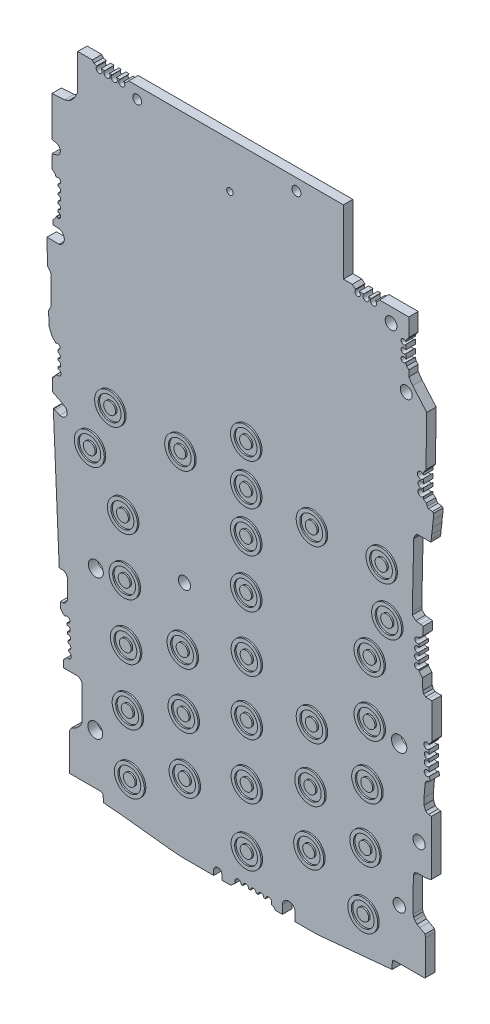
SolidWorks part; units mm, degrees
material "Plastique personnalisé"
ref_plane "Plan de face" through (0, 0, 0) normal (0, 0, 1) x (1, 0, 0)
ref_plane "Plan de dessus" through (0, 0, 0) normal (0, 1, 0) x (1, 0, 0)
ref_plane "Plan de droite" through (0, 0, 0) normal (1, 0, 0) x (0, 0, -1)
sketch "pcbmain" plane through (0, 0, 0) normal (0, 0, 1) x (1, 0, 0)
  line L0 (-26.3476, 56.3002) -> (18.5524, 56.3002) construction
  line L1 (-26.3472, 56.3293) -> (-23.9276, 56.3293)
  line L2 (18.595, 45.4298) -> (20.1113, 45.4298)
  line L3 (18.595, 56.3293) -> (18.595, 45.4298)
  line L4 (29.6758, 45.4298) -> (29.6758, 42.4054)
  line L5 (29.6758, 36.6277) -> (30.333, 35.6864)
  line L6 (30.333, 35.6864) -> (32.1199, 33.6174)
  line L7 (32.1199, 33.6174) -> (32.7131, 32.9305)
  line L8 (32.7131, 32.9305) -> (32.5843, 24.4781)
  line L9 (32.5843, 24.4781) -> (32.1653, 23.839)
  line L10 (32.1653, 23.839) -> (32.1653, 23.4305)
  line L11 (32.1653, 20.2857) -> (32.1653, 19.9086)
  line L12 (32.1653, 19.9086) -> (32.6305, 19.6035)
  line L13 (32.6305, 19.6035) -> (32.804, 19.1871)
  line L14 (33.0248, 18.9629) -> (33.6866, 18.8922)
  line L15 (33.6866, 18.8922) -> (33.876, 18.717)
  line L16 (33.876, 18.717) -> (33.876, 17.8058)
  line L17 (33.876, 17.8058) -> (33.7813, 17.8058)
  line L18 (33.7813, 17.8058) -> (33.7082, 16.5757)
  line L19 (33.7082, 16.5757) -> (33.5539, 15.419)
  line L20 (33.5539, 15.419) -> (33.4978, 14.7416)
  line L21 (33.4978, 14.7416) -> (33.4001, 14.2515)
  line L22 (33.4001, 14.2515) -> (31.0026, 14.2515)
  line L23 (31.0026, 14.2515) -> (30.6972, 13.7858)
  line L24 (30.6972, 13.7858) -> (30.5206, 13.3921)
  line L25 (30.5206, 13.3921) -> (30.506, 13.216)
  line L26 (30.506, 13.216) -> (30.2731, 2.4736)
  line L27 (30.2731, 2.4736) -> (30.2731, 1.9888)
  line L28 (30.2731, 1.9888) -> (30.5221, 1.7586)
  line L29 (30.5221, 1.7586) -> (30.8499, 1.4554)
  line L30 (30.8499, 1.4554) -> (31.0993, 1.4057)
  line L31 (31.0993, 1.4057) -> (31.6928, 1.3565)
  line L32 (31.6928, 1.3565) -> (32.1199, 1.2715)
  line L33 (32.1199, 1.2715) -> (32.1199, -0.1245)
  line L34 (32.1199, -0.1245) -> (31.8538, -0.3542)
  line L35 (31.8538, -0.3542) -> (31.7258, -0.5495)
  line L36 (31.7258, -0.5495) -> (31.3961, -0.6869)
  line L37 (31.3961, -0.6869) -> (31.3961, -0.9137)
  line L38 (31.3961, -5.654) -> (31.9868, -6.338)
  line L39 (31.9868, -6.338) -> (32.0491, -8.1942)
  line L40 (32.0491, -8.1942) -> (32.2013, -8.6516)
  line L41 (32.2013, -8.6516) -> (32.5523, -8.8818)
  line L42 (32.5523, -8.8818) -> (32.9753, -8.9168)
  line L43 (32.9753, -8.9168) -> (33.6311, -8.9168)
  line L44 (33.6311, -8.9168) -> (33.6311, -14.8864)
  line L45 (33.6311, -14.8864) -> (33.1333, -15.5093)
  line L46 (33.1333, -15.5093) -> (33.1333, -15.6135)
  line L47 (33.1333, -20.2606) -> (33.3188, -20.8179)
  line L48 (33.3188, -20.8179) -> (33.1333, -20.9781)
  line L49 (33.1333, -20.9781) -> (32.7638, -21.1012)
  line L50 (32.7638, -21.1012) -> (32.4789, -21.4576)
  line L51 (32.4789, -21.4576) -> (32.43, -21.7035)
  line L52 (32.43, -21.7035) -> (32.2548, -23.8175)
  line L53 (32.2548, -23.8175) -> (32.2548, -24.9106)
  line L54 (32.2548, -24.9106) -> (32.5523, -25.6246)
  line L55 (32.5523, -25.6246) -> (33.0248, -25.8955)
  line L56 (33.0248, -25.8955) -> (33.4978, -25.9347)
  line L57 (33.4978, -25.9347) -> (33.4978, -35.191)
  line L58 (33.4978, -35.191) -> (33.1823, -35.3224)
  line L59 (33.1823, -35.3224) -> (32.5523, -35.4198)
  line L60 (32.5523, -35.4198) -> (31.0993, -35.4198)
  line L61 (31.0993, -35.4198) -> (30.686, -35.5921)
  line L62 (30.686, -35.5921) -> (30.4941, -35.9268)
  line L63 (30.4941, -35.9268) -> (30.4394, -36.2015)
  line L64 (30.4394, -36.2015) -> (30.3976, -41.7883)
  line L65 (30.3976, -41.7883) -> (30.4941, -42.2439)
  line L66 (30.4941, -42.2439) -> (30.7305, -42.5825)
  line L67 (30.7305, -42.5825) -> (31.0716, -42.9775)
  line L68 (31.0716, -42.9775) -> (31.534, -43.2426)
  line L69 (31.534, -43.2426) -> (32.43, -43.7347)
  line L70 (32.43, -43.7347) -> (32.5255, -44.1857)
  line L71 (32.5255, -44.1857) -> (32.4811, -50.1182)
  line L72 (32.4811, -50.1182) -> (32.3424, -50.215)
  line L73 (32.3424, -50.215) -> (27.1201, -50.215)
  line L74 (27.1201, -50.215) -> (26.9245, -50.384)
  line L75 (26.9245, -50.384) -> (26.8778, -50.6183)
  line L76 (26.8778, -50.6183) -> (26.854, -51.7168)
  line L77 (26.854, -51.7168) -> (14.0715, -52.9243)
  line L78 (14.0715, -52.9243) -> (12.4897, -52.9243)
  line L79 (12.4897, -52.9243) -> (10.4248, -52.9243)
  line L80 (10.4248, -52.9243) -> (10.4248, -51.5129)
  line L82 (8.2651, -51.5129) -> (8.2651, -52.9243)
  line L83 (8.2651, -52.9243) -> (7.0763, -52.9243)
  line L84 (7.0763, -52.9243) -> (6.7493, -52.5455)
  line L85 (6.7493, -52.5455) -> (6.4591, -52.4154)
  line L86 (6.4591, -52.4154) -> (6.4591, -52.0567)
  line L87 (5.429, -52.0567) -> (5.0907, -52.0567)
  line L88 (0.2185, -52.0567) -> (0.2185, -52.4154)
  line L89 (0.2185, -52.4154) -> (-0.4956, -53.0321)
  line L90 (-0.4956, -53.0321) -> (-1.9859, -53.0321)
  line L91 (-1.9859, -53.0321) -> (-1.9859, -52.236)
  line L93 (-3.3634, -52.236) -> (-3.3634, -53.0321)
  line L94 (-3.3634, -53.0321) -> (-8.7561, -53.0321)
  line L95 (-8.7561, -53.0321) -> (-11.0114, -52.8452)
  line L96 (-11.0114, -52.8452) -> (-17.1621, -52.1575)
  line L97 (-17.1621, -52.1575) -> (-19.1333, -51.937)
  line L98 (-19.1333, -51.937) -> (-21.3313, -51.7549)
  line L99 (-21.3313, -51.7549) -> (-22.056, -51.6739)
  line L100 (-22.056, -51.6739) -> (-22.0902, -50.6556)
  line L101 (-22.0902, -50.6556) -> (-22.1767, -50.448)
  line L102 (-22.1767, -50.448) -> (-22.3284, -50.3267)
  line L103 (-22.3284, -50.3267) -> (-22.6489, -50.2629)
  line L104 (-22.6489, -50.2629) -> (-27.796, -50.2629)
  line L105 (-27.796, -50.2629) -> (-27.796, -43.9395)
  line L106 (-27.796, -43.9395) -> (-27.4814, -43.4597)
  line L107 (-27.4814, -43.4597) -> (-27.0528, -43.2426)
  line L108 (-27.0528, -43.2426) -> (-26.7348, -43.11)
  line L109 (-26.7348, -43.11) -> (-26.2801, -42.6873)
  line L110 (-26.2801, -42.6873) -> (-25.9044, -42.2809)
  line L111 (-25.9044, -42.2809) -> (-25.7484, -41.9332)
  line L112 (-25.7484, -41.9332) -> (-25.6965, -41.8175)
  line L113 (-25.6965, -41.8175) -> (-25.653, -35.9963)
  line L114 (-25.653, -35.9963) -> (-25.7326, -35.8052)
  line L115 (-25.7326, -35.8052) -> (-25.9044, -35.6064)
  line L116 (-25.9044, -35.6064) -> (-26.0562, -35.4659)
  line L117 (-26.0562, -35.4659) -> (-26.1749, -35.3711)
  line L118 (-26.1749, -35.3711) -> (-26.3472, -35.2938)
  line L119 (-26.3472, -35.2938) -> (-28.8359, -35.2938)
  line L120 (-28.8359, -35.2938) -> (-28.8359, -34.1043)
  line L121 (-28.8359, -34.1043) -> (-28.4975, -33.812)
  line L122 (-28.4975, -33.812) -> (-28.2801, -33.54)
  line L123 (-28.2801, -33.54) -> (-28.1038, -33.5233)
  line L124 (-28.1038, -33.5233) -> (-27.8558, -33.5233)
  line L125 (-27.9317, -32.4351) -> (-27.9505, -32.1647)
  line L126 (-28.2801, -27.4401) -> (-28.6667, -27.6012)
  line L127 (-28.6667, -27.6012) -> (-28.8059, -27.4401)
  line L128 (-28.8059, -27.4401) -> (-29.3011, -26.8667)
  line L129 (-29.3011, -26.8667) -> (-29.3011, -25.7861)
  line L130 (-29.3011, -25.7861) -> (-28.8822, -25.7861)
  line L131 (-28.8822, -25.7861) -> (-28.5457, -25.6459)
  line L132 (-28.5457, -25.6459) -> (-28.3448, -25.4286)
  line L133 (-28.3448, -25.4286) -> (-28.1621, -25.0959)
  line L134 (-28.1621, -25.0959) -> (-28.1402, -24.9862)
  line L135 (-28.1402, -24.9862) -> (-28.1402, -21.7303)
  line L136 (-28.1402, -21.7303) -> (-28.2018, -21.5453)
  line L137 (-28.2018, -21.5453) -> (-28.3568, -21.3025)
  line L138 (-28.3568, -21.3025) -> (-28.5305, -21.1418)
  line L139 (-28.5305, -21.1418) -> (-28.6817, -21.0588)
  line L140 (-28.6817, -21.0588) -> (-28.8654, -21.0019)
  line L141 (-28.8654, -21.0019) -> (-29.4497, -21.0019)
  line L142 (-29.4497, -21.0019) -> (-29.5384, -20.8993)
  line L143 (-29.5384, -20.8993) -> (-30.539, 1.9081)
  line L144 (-30.539, 1.9081) -> (-30.4443, 1.9081)
  line L145 (-30.4443, 1.9081) -> (-30.2416, 1.7968)
  line L147 (-29.2742, 3.5581) -> (-30.6939, 4.2682)
  line L148 (-30.6939, 4.2682) -> (-30.716, 5.2591)
  line L149 (-30.716, 5.2591) -> (-30.716, 6.3629)
  line L150 (-30.716, 6.3629) -> (-30.548, 6.4188)
  line L151 (-30.548, 6.4188) -> (-30.1481, 6.8512)
  line L152 (-30.1481, 6.8512) -> (-30.0803, 7.0704)
  line L153 (-30.0803, 7.0704) -> (-30.0057, 7.118)
  line L154 (-30.0057, 7.118) -> (-29.7579, 7.118)
  line L155 (-29.7579, 8.0616) -> (-29.7579, 8.3754)
  line L156 (-29.7579, 11.8098) -> (-30.1273, 11.6869)
  line L157 (-30.1273, 11.6869) -> (-30.632, 12.2713)
  line L158 (-30.632, 12.2713) -> (-30.8474, 12.5207)
  line L159 (-30.8474, 12.5207) -> (-30.9767, 12.909)
  line L160 (-30.9767, 12.909) -> (-31.2457, 13.5545)
  line L161 (-31.2457, 13.5545) -> (-31.3467, 15.8567)
  line L162 (-31.3467, 15.8567) -> (-31.0827, 16.3846)
  line L163 (-31.0827, 16.3846) -> (-30.9593, 16.5636)
  line L164 (-30.9593, 16.5636) -> (-30.9593, 21.4877)
  line L165 (-30.9593, 21.4877) -> (-31.0481, 21.7006)
  line L166 (-31.0481, 21.7006) -> (-31.2804, 22.0359)
  line L167 (-31.2804, 22.0359) -> (-31.5199, 22.2878)
  line L168 (-31.5199, 22.2878) -> (-31.6133, 26.4777)
  line L169 (-31.6133, 26.4777) -> (-29.5384, 26.4777)
  line L171 (-29.5384, 28.7595) -> (-30.6062, 28.788)
  line L172 (-30.6062, 28.788) -> (-30.6062, 29.5385)
  line L173 (-30.6062, 29.5385) -> (-30.1378, 30.045)
  line L174 (-30.1378, 30.045) -> (-30.0597, 30.2974)
  line L175 (-30.0597, 30.2974) -> (-29.9426, 30.2974)
  line L176 (-29.9426, 30.2974) -> (-29.7525, 30.2023)
  line L177 (-29.7525, 30.2023) -> (-29.7082, 30.2023)
  line L178 (-29.7082, 31.0839) -> (-29.7082, 31.5125)
  line L179 (-29.7082, 36.2036) -> (-30.0597, 36.0571)
  line L180 (-30.0597, 36.0571) -> (-30.2416, 36.4937)
  line L181 (-30.2416, 36.4937) -> (-30.4917, 36.7249)
  line L182 (-30.4917, 36.7249) -> (-30.7397, 36.849)
  line L183 (-30.7397, 36.849) -> (-30.716, 39.2001)
  line L184 (-30.716, 39.2001) -> (-30.4443, 39.219)
  line L185 (-30.4443, 39.219) -> (-30.1506, 39.3168)
  line L187 (-30.1506, 41.1223) -> (-30.4708, 41.1861)
  line L188 (-30.4708, 41.1861) -> (-30.7633, 41.2444)
  line L189 (-30.7633, 41.2444) -> (-30.7817, 41.2614)
  line L190 (-30.7817, 41.2614) -> (-30.7817, 47.9834)
  line L191 (-30.7817, 47.9834) -> (-28.6061, 48.1351)
  line L192 (-28.6061, 48.1351) -> (-27.9329, 48.3593)
  line L193 (-27.9329, 48.3593) -> (-27.3741, 48.7463)
  line L194 (-27.3741, 48.7463) -> (-26.9107, 49.3263)
  line L195 (-26.9107, 49.3263) -> (-26.6074, 49.9325)
  line L196 (-26.6074, 49.9325) -> (-26.4023, 50.3426)
  line L197 (-26.4023, 50.3426) -> (-26.4023, 56.3293)
  line L198 (-26.4023, 56.3293) -> (-26.3472, 56.3293)
  line L199 (-29.7082, 32.3376) -> (-29.7082, 32.7575)
  line L200 (-29.7082, 33.5925) -> (-29.7082, 33.935)
  line L201 (-29.7082, 34.8538) -> (-29.7082, 35.2532)
  line L202 (-29.7579, 10.5366) -> (-29.7579, 10.9255)
  line L203 (-29.7579, 9.3433) -> (-29.7579, 9.6306)
  line L204 (-29.2742, 3.5581) -> (-28.714, 3.2243)
  line L205 (-30.2416, 1.7968) -> (-29.4497, 1.4304)
  line L206 (-28.1894, -28.7393) -> (-28.2141, -28.3852)
  line L207 (-28.1, -30.0214) -> (-28.1266, -29.6408)
  line L208 (-28.0144, -31.2488) -> (-28.0402, -30.8797)
  line L209 (1.5746, -52.0567) -> (1.2979, -52.0567)
  line L210 (2.8868, -52.0567) -> (2.5382, -52.0567)
  line L211 (4.1681, -52.0567) -> (3.7735, -52.0567)
  line L212 (33.1333, -16.2809) -> (33.1333, -17.0014)
  line L213 (33.1333, -17.638) -> (33.1333, -18.1861)
  line L214 (33.1333, -18.8447) -> (33.1333, -19.6226)
  line L215 (31.3961, -5.4452) -> (31.3961, -5.654)
  line L216 (31.3961, -4.0963) -> (31.3961, -4.7104)
  line L217 (31.3961, -2.9315) -> (31.3961, -3.4257)
  line L218 (31.3961, -1.6844) -> (31.3961, -2.2197)
  line L219 (32.1653, 22.9543) -> (32.1653, 22.1563)
  line L220 (32.1653, 21.6104) -> (32.1481, 20.9645)
  line L221 (29.6758, 42.4054) -> (29.1821, 41.7726)
  line L222 (29.1821, 41.7726) -> (29.1821, 41.5324)
  line L223 (29.1821, 38.4338) -> (29.2984, 37.9974)
  line L224 (29.2984, 37.9974) -> (29.6758, 37.6555)
  line L225 (29.6758, 37.6555) -> (29.6758, 36.6277)
  line L226 (29.1821, 38.4923) -> (29.1821, 38.4338)
  line L227 (29.1821, 39.7817) -> (29.1821, 38.9651)
  line L228 (29.1821, 41.157) -> (29.1821, 40.3433)
  line L229 (20.1113, 45.4298) -> (20.6301, 44.9722)
  line L230 (20.6301, 44.9722) -> (20.7217, 44.9722)
  line L231 (24.0446, 44.9722) -> (24.4312, 45.0502)
  line L232 (24.4312, 45.0502) -> (24.7058, 45.4298)
  line L233 (24.7058, 45.4298) -> (29.6758, 45.4298)
  line L234 (22.8375, 44.9722) -> (23.3258, 44.9722)
  line L235 (21.2642, 44.9722) -> (22.0339, 44.9722)
  line L236 (-23.9276, 56.3293) -> (-23.6646, 55.9528)
  line L237 (-23.6646, 55.9528) -> (-23.2013, 55.8026)
  line L238 (-23.2013, 55.8026) -> (-23.1282, 55.8026)
  line L239 (-18.6306, 55.8026) -> (-18.28, 55.8026)
  line L240 (-18.28, 55.8026) -> (-17.7728, 56.3293)
  line L241 (-17.7728, 56.3293) -> (18.595, 56.3293)
  line L242 (-19.857, 55.8026) -> (-19.2665, 55.8026)
  line L243 (-21.0361, 55.8026) -> (-20.5919, 55.8026)
  line L244 (-22.4342, 55.8026) -> (-21.8283, 55.8026)
  line L245 (32.1481, 20.2857) -> (32.1653, 20.2857)
  arc A0 (32.804, 19.1871) -> (33.0248, 18.9629) centre (33.1926, 19.349) ccw
  circle A1 centre (-16.3223, 54.33) radius 0.7602
  circle A2 centre (10.6479, 54.3822) radius 0.7591
  circle A3 centre (26.6739, 43.0034) radius 0.9966
  circle A4 centre (29.24, 34.1762) radius 1.0128
  circle A5 centre (-0.618, 48.6766) radius 0.5512
  circle A6 centre (-8.3261, -12.5822) radius 1.0254
  circle A7 centre (31.417, -30.7219) radius 1.0323
  circle A8 centre (28.062, -41.6944) radius 1.0418
  circle A9 centre (-23.4265, -41.7117) radius 1.257
  circle A10 centre (-23.3399, -17.9875) radius 1.2695
  circle A11 centre (28.0374, -17.9774) radius 1.2998
  arc A12 (-30.1506, 41.1223) -> (-30.1506, 39.3168) centre (-30.2618, 40.2196) cw
  arc A13 (-29.7082, 36.2036) -> (-29.7082, 35.2532) centre (-29.7648, 35.7284) cw
  arc A14 (-29.7082, 34.8538) -> (-29.7082, 33.935) centre (-29.7479, 34.3944) cw
  arc A15 (-29.7082, 33.5925) -> (-29.7082, 32.7575) centre (-29.7082, 33.175) cw
  arc A16 (-29.7082, 32.3376) -> (-29.7082, 31.5125) centre (-29.7082, 31.925) cw
  arc A17 (-29.7082, 31.0839) -> (-29.7082, 30.2023) centre (-29.7359, 30.6431) cw
  arc A18 (-29.5384, 28.7595) -> (-29.5384, 26.4777) centre (-29.861, 27.6186) cw
  arc A19 (-29.7579, 11.8098) -> (-29.7579, 10.9255) centre (-29.8293, 11.3677) cw
  arc A20 (-29.7579, 10.5366) -> (-29.7579, 9.6306) centre (-29.8009, 10.0836) cw
  arc A21 (-29.7579, 9.3433) -> (-29.7579, 8.3754) centre (-29.7681, 8.8594) cw
  arc A22 (-29.7579, 8.0616) -> (-29.7579, 7.118) centre (-29.7109, 7.5898) cw
  arc A23 (-28.714, 3.2243) -> (-29.4497, 1.4304) centre (-29.1748, 2.3655) cw
  arc A24 (-28.2801, -27.4401) -> (-28.2141, -28.3852) centre (-28.1992, -27.9093) cw
  arc A25 (-28.1894, -28.7393) -> (-28.1266, -29.6408) centre (-28.1244, -29.1877) cw
  arc A26 (-28.1, -30.0214) -> (-28.0402, -30.8797) centre (-28.0411, -30.4485) cw
  arc A27 (-28.0144, -31.2488) -> (-27.9505, -32.1647) centre (-28.0281, -31.7099) cw
  arc A28 (-27.9317, -32.4351) -> (-27.8558, -33.5233) centre (-28.079, -32.9921) cw
  arc A29 (-3.3634, -52.236) -> (-1.9859, -52.236) centre (-2.6747, -52.1987) cw
  arc A30 (0.2185, -52.0567) -> (1.2979, -52.0567) centre (0.7582, -52.0361) cw
  arc A31 (1.5746, -52.0567) -> (2.5382, -52.0567) centre (2.0564, -51.9987) cw
  arc A32 (2.8868, -52.0567) -> (3.7735, -52.0567) centre (3.3301, -51.9945) cw
  arc A33 (4.1681, -52.0567) -> (5.0907, -52.0567) centre (4.6294, -52.0122) cw
  arc A34 (5.429, -52.0567) -> (6.4591, -52.0567) centre (5.944, -52.0459) cw
  arc A35 (8.2651, -51.5129) -> (10.4248, -51.5129) centre (9.345, -51.5311) cw
  arc A36 (33.1333, -15.6135) -> (33.1333, -16.2809) centre (32.7495, -15.9472) ccw
  arc A37 (33.1333, -17.0014) -> (33.1333, -17.638) centre (32.781, -17.3197) ccw
  arc A38 (33.1333, -18.1861) -> (33.1333, -18.8447) centre (32.7816, -18.5154) ccw
  arc A39 (33.1333, -19.6226) -> (33.1333, -20.2606) centre (32.7675, -19.9416) ccw
  arc A40 (31.3961, -0.9137) -> (31.3961, -1.6844) centre (31.1428, -1.299) ccw
  arc A41 (31.3961, -2.9315) -> (31.3961, -2.2197) centre (31.1086, -2.5756) cw
  arc A42 (31.3961, -5.4452) -> (31.3961, -4.7104) centre (31.1107, -5.0778) cw
  arc A43 (31.3961, -4.0963) -> (31.3961, -3.4257) centre (31.0925, -3.761) cw
  arc A44 (32.1653, 23.4305) -> (32.1653, 22.9543) centre (31.678, 23.1924) ccw
  arc A45 (32.1653, 22.1563) -> (32.1653, 21.6104) centre (31.7325, 21.8834) ccw
  arc A46 (32.1481, 20.9645) -> (32.1481, 20.2857) centre (31.7418, 20.6251) ccw
  arc A47 (29.1821, 41.5324) -> (29.1821, 41.157) centre (28.7945, 41.3447) ccw
  arc A48 (29.1821, 40.3433) -> (29.1821, 39.7817) centre (28.8184, 40.0625) ccw
  arc A49 (29.1821, 38.9651) -> (29.1821, 38.4923) centre (28.8108, 38.7287) ccw
  arc A50 (20.7217, 44.9722) -> (21.2642, 44.9722) centre (20.9929, 44.5846) ccw
  arc A51 (22.0339, 44.9722) -> (22.8375, 44.9722) centre (22.4357, 44.6188) ccw
  arc A52 (23.3258, 44.9722) -> (24.0446, 44.9722) centre (23.6852, 44.5848) ccw
  arc A53 (-23.1282, 55.8026) -> (-22.4342, 55.8026) centre (-22.7812, 55.4353) ccw
  arc A54 (-21.8283, 55.8026) -> (-21.0361, 55.8026) centre (-21.4322, 55.444) ccw
  arc A55 (-20.5919, 55.8026) -> (-19.857, 55.8026) centre (-20.2245, 55.4206) ccw
  arc A56 (-19.2665, 55.8026) -> (-18.6306, 55.8026) centre (-18.9486, 55.3964) ccw
  dimension "D1" = 44.9
sketch "buttons" plane through (0, 0, 0) normal (0, 0, 1) x (1, 0, 0)
  circle A0 centre (2.268, 13.4844) radius 1.0026
  circle A1 centre (2.268, 13.4844) radius 1.939
  circle A2 centre (2.268, 13.4844) radius 2.542
  circle A3 centre (-8.8835, 6.5159) radius 1.0026
  circle A4 centre (-8.8835, 6.4519) radius 1.939
  circle A5 centre (-8.8835, 6.4519) radius 2.542
  circle A6 centre (-20.7514, 6.9567) radius 1.0026
  circle A7 centre (-20.7514, 6.9567) radius 1.939
  circle A8 centre (-20.7514, 6.9567) radius 2.542
  circle A9 centre (-24.1954, -0.6541) radius 1.0026
  circle A10 centre (-24.1954, -0.6541) radius 1.939
  circle A11 centre (-24.1954, -0.6541) radius 2.542
  circle A12 centre (-18.5821, -7.6912) radius 1.0026
  circle A13 centre (-18.5821, -7.6912) radius 1.939
  circle A14 centre (-18.5821, -7.6912) radius 2.542
  circle A15 centre (-18.2973, -17.1276) radius 1.0026
  circle A16 centre (-18.2973, -17.1276) radius 1.939
  circle A17 centre (-18.2973, -17.1276) radius 2.542
  circle A18 centre (-18.0862, -26.5243) radius 1.0026
  circle A19 centre (-18.0862, -26.5243) radius 1.939
  circle A20 centre (-18.0862, -26.5243) radius 2.542
  circle A21 centre (-17.7802, -35.9513) radius 1.0026
  circle A22 centre (-17.7802, -35.9513) radius 1.939
  circle A23 centre (-17.7802, -35.9513) radius 2.542
  circle A24 centre (-17.4115, -45.8962) radius 1.0026
  circle A25 centre (-17.4115, -45.8962) radius 1.939
  circle A26 centre (-17.4115, -45.8962) radius 2.542
  circle A27 centre (-8.4816, -22.3926) radius 1.0026
  circle A28 centre (-8.4816, -22.3926) radius 1.939
  circle A29 centre (-8.4816, -22.3926) radius 2.542
  circle A30 centre (-8.3165, -31.7393) radius 1.0026
  circle A31 centre (-8.3165, -31.7393) radius 1.939
  circle A32 centre (-8.3165, -31.7393) radius 2.542
  circle A33 centre (-8.1401, -41.1372) radius 1.0026
  circle A34 centre (-8.1401, -41.1372) radius 1.939
  circle A35 centre (-8.1401, -41.1372) radius 2.542
  circle A36 centre (2.268, 6.5159) radius 1.0026
  circle A37 centre (2.268, 6.5159) radius 1.939
  circle A38 centre (2.268, 6.5159) radius 2.542
  circle A39 centre (2.268, -0.3952) radius 1.0026
  circle A40 centre (2.268, -0.3952) radius 1.939
  circle A41 centre (2.268, -0.3952) radius 2.542
  circle A42 centre (2.268, -8.6246) radius 1.0026
  circle A43 centre (2.268, -8.6246) radius 1.939
  circle A44 centre (2.268, -8.6246) radius 2.542
  circle A45 centre (2.365, -18.027) radius 1.0026
  circle A46 centre (2.365, -18.027) radius 1.939
  circle A47 centre (2.365, -18.027) radius 2.542
  circle A48 centre (2.365, -27.3118) radius 1.0026
  circle A49 centre (2.365, -27.3118) radius 1.939
  circle A50 centre (2.365, -27.3118) radius 2.542
  circle A51 centre (2.365, -36.7277) radius 1.0026
  circle A52 centre (2.365, -36.7277) radius 1.939
  circle A53 centre (2.365, -36.7277) radius 2.542
  circle A54 centre (2.365, -46.5823) radius 1.0026
  circle A55 centre (2.365, -46.5823) radius 1.939
  circle A56 centre (2.365, -46.5823) radius 2.542
  circle A57 centre (13.3975, 6.5159) radius 1.0026
  circle A58 centre (13.3975, 6.5159) radius 1.939
  circle A59 centre (13.3975, 6.5159) radius 2.542
  circle A60 centre (13.3975, -22.3926) radius 1.0026
  circle A61 centre (13.3975, -22.3926) radius 1.939
  circle A62 centre (13.3975, -22.3926) radius 2.542
  circle A63 centre (13.1513, -31.7393) radius 1.0026
  circle A64 centre (13.1513, -31.7393) radius 1.939
  circle A65 centre (13.1513, -31.7393) radius 2.542
  circle A66 centre (12.9619, -41.1372) radius 1.0026
  circle A67 centre (12.9619, -41.1372) radius 1.939
  circle A68 centre (12.9619, -41.1372) radius 2.542
  circle A69 centre (25.2131, 6.9567) radius 1.0026
  circle A70 centre (25.2131, 6.9567) radius 1.939
  circle A71 centre (25.2131, 6.9567) radius 2.542
  circle A72 centre (26.1653, -0.7804) radius 1.0026
  circle A73 centre (26.1653, -0.7804) radius 1.939
  circle A74 centre (26.1653, -0.7804) radius 2.542
  circle A75 centre (23.1899, -7.6912) radius 1.0026
  circle A76 centre (23.1899, -7.6912) radius 1.939
  circle A77 centre (23.1899, -7.6912) radius 2.542
  circle A78 centre (23.1899, -17.1276) radius 1.0026
  circle A79 centre (23.1899, -17.1276) radius 1.939
  circle A80 centre (23.1899, -17.1276) radius 2.542
  circle A81 centre (22.7905, -26.5243) radius 1.0026
  circle A82 centre (22.7905, -26.5243) radius 1.939
  circle A83 centre (22.7905, -26.5243) radius 2.542
  circle A84 centre (22.4764, -35.9513) radius 1.0026
  circle A85 centre (22.4764, -35.9513) radius 1.939
  circle A86 centre (22.4764, -35.9513) radius 2.542
  circle A87 centre (22.1279, -45.8962) radius 1.0026
  circle A88 centre (22.1279, -45.8962) radius 1.939
  circle A89 centre (22.1279, -45.8962) radius 2.542
  point P14 (-18.0862, -26.5243)
  point P30 (-17.7802, -35.9513)
  point P39 (-17.4115, -45.8962)
  point P44 (-8.4816, -22.3926)
  point P49 (-8.3165, -31.7393)
  point P54 (-8.1401, -41.1372)
  point P59 (2.268, 6.5159)
  point P64 (2.268, -0.3952)
  point P69 (2.268, -8.6246)
  point P74 (2.365, -18.027)
  point P79 (2.365, -27.3118)
  point P84 (2.365, -36.7277)
  point P89 (2.365, -46.5823)
  point P94 (13.3975, 6.5159)
  point P99 (13.3975, -22.3926)
  point P104 (13.1513, -31.7393)
  point P109 (12.9619, -41.1372)
  point P114 (25.2131, 6.9567)
  point P119 (26.1653, -0.7804)
  point P124 (23.1921, -7.7571)
  point P125 (23.1899, -7.6912)
  point P130 (23.1899, -17.1276)
  point P135 (22.7905, -26.5243)
  point P140 (22.4764, -35.9513)
  point P145 (22.1279, -45.8962)
extrude "Boss.-Extru.1" add sketch "pcbmain" against normal blind 1.6
extrude "Boss.-Extru.2" add sketch "buttons" along normal blind 0.25 contours A2 A1 | A0 | A6 | A8 A7 | A11 A10 | A9 | A3 | A5 A4 | A38 A37 | A36 | A41 A40 | A39 | A14 A13 | A12 | A59 A58 | A57 | A69 | A71 A70 | A72 | A74 A73 | A44 A43 | A42 | A75 | A77 A76 | A15 | A17 A16 | A29 A28 | A27 | A18 | A20 A19 | A45 | A47 A46 | A80 A79 | A78 | A60 | A62 A61 | A83 A82 | A81 | A48 | A50 A49 | A63 | A65 A64 | A32 A31 | A30 | A23 A22 | A21 | A33 | A35 A34 | A26 A25 | A24 | A53 A52 | A51 | A86 A85 | A84 | A68 A67 | A66 | A54 | A56 A55 | A89 A88 | A87
